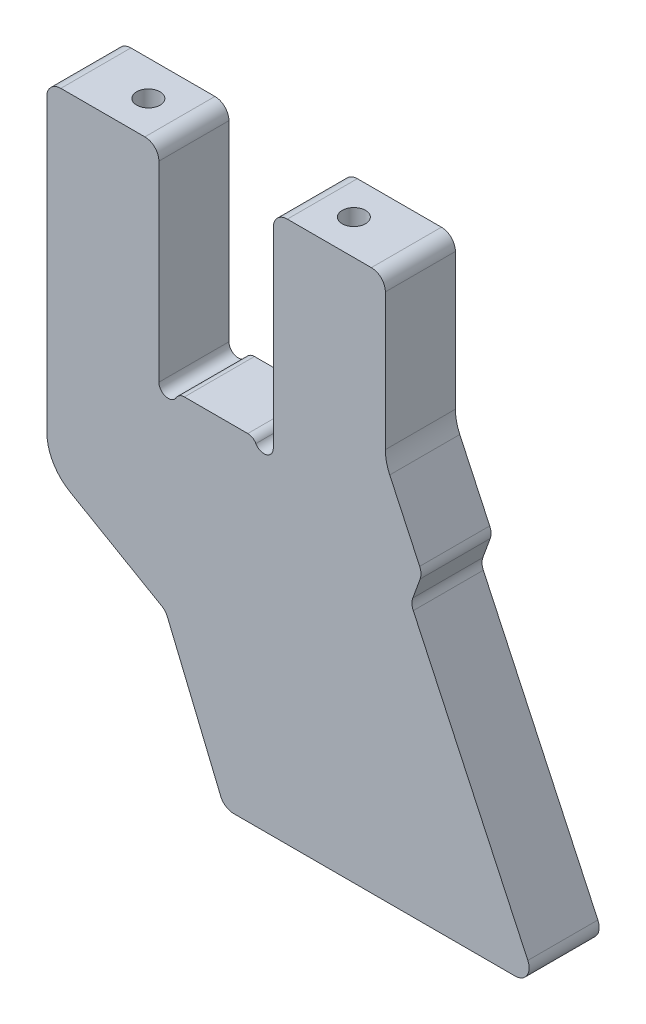
SolidWorks part; units mm, degrees
ref_plane "Plane1" through (0, 0, 0) normal (0, 0, 1) x (1, 0, 0)
ref_plane "Plane2" through (0, 0, 0) normal (0, 1, 0) x (1, 0, 0)
ref_plane "Plane3" through (0, 0, 0) normal (1, 0, 0) x (0, 0, -1)
sketch "Sketch1" plane through (0, 0, 0) normal (0, 0, 1) x (1, 0, 0)
  line L0 (0, 0) -> (0, 44) construction
  line L1 (33.25, 44) -> (15.25, 44)
  line L2 (-33.25, 44) -> (-15.25, 44)
  line L3 (6.7859, 0) -> (-6.7859, 0)
  line L4 (-11.6863, -41.1819) -> (-31.25, -29.8868)
  line L5 (3.7545, -72) -> (64.0409, -72)
  line L6 (-36.25, 41) -> (-36.25, -21.2265)
  line L7 (-10.4147, -42.6319) -> (0.9829, -70.1481)
  line L8 (42.1292, -12.8323) -> (43.6976, -8.5231)
  line L9 (12.25, 41) -> (12.25, 0)
  line L10 (-12.25, 41) -> (-12.25, 0)
  line L11 (36.25, 11.7444) -> (36.25, 41)
  line L12 (43.5974, -6.2292) -> (37.1869, 7.5182)
  line L15 (42.2293, -15.1262) -> (66.7599, -67.7321)
  arc A0 (-12.25, 41) -> (-15.25, 44) centre (-15.25, 41) ccw
  arc A1 (12.25, 0) -> (8.5179, -1) centre (10.25, 0) cw
  arc A2 (8.5179, -1) -> (6.7859, 0) centre (6.7859, -2) ccw
  arc A3 (12.25, 41) -> (15.25, 44) centre (15.25, 41) cw
  arc A4 (-8.5179, -1) -> (-6.7859, 0) centre (-6.7859, -2) cw
  arc A5 (-12.25, 0) -> (-8.5179, -1) centre (-10.25, 0) ccw
  arc A6 (-36.25, 41) -> (-33.25, 44) centre (-33.25, 41) cw
  arc A7 (36.25, 41) -> (33.25, 44) centre (33.25, 41) ccw
  arc A8 (-11.6863, -41.1819) -> (-10.4147, -42.6319) centre (-13.1863, -43.7799) cw
  arc A9 (64.0409, -72) -> (66.7599, -67.7321) centre (64.0409, -69) ccw
  arc A10 (-31.25, -29.8868) -> (-36.25, -21.2265) centre (-26.25, -21.2265) cw
  arc A11 (0.9829, -70.1481) -> (3.7545, -72) centre (3.7545, -69) ccw
  arc A12 (37.1869, 7.5182) -> (36.25, 11.7444) centre (46.25, 11.7444) cw
  arc A13 (43.6976, -8.5231) -> (43.5974, -6.2292) centre (40.8785, -7.497) ccw
  arc A14 (42.1292, -12.8323) -> (42.2293, -15.1262) centre (44.9482, -13.8584) ccw
  point P7 (-12.25, 44)
  point P22 (68.75, -72)
  point P23 (12.25, 44)
  point P28 (0, 0)
  point P31 (-36.25, -27)
  point P37 (1.75, -72)
  point P45 (36.25, -2.3035)
  point P53 (41.7042, -14)
  dimension "D2" = 22.5
  dimension "D9" = 116
  dimension "D10" = 105
  dimension "D7" = 60
  dimension "D12" = 71
  dimension "D13" = 3
  dimension "D14" = 10
  dimension "D15" = 58
  dimension "D16" = 3
  dimension "D17" = 24
  dimension "D19" = 3
  dimension "D11" = 2
  dimension "D22" = 10
  dimension "D23" = 3
  dimension "D3" = 25
  dimension "D4" = 24.5
  dimension "D5" = 67
  dimension "D6" = 72.5
  dimension "D8" = 44
  dimension "D18" = 24
  dimension "D20" = 5
  dimension "D21" = 45
extrude "Base-Extrude" add sketch "Sketch1" against normal blind 15
hole_wizard "Hole1" positions "Sketch3" profile "Sketch2" legacy
sketch "Sketch3" plane through (0, 44, 0) normal (0, 1, 0) x (-1, 0, 0)
  line L1 (15.25, -15) -> (33.25, -15) construction
  line L3 (0, 0) -> (0, -15) construction
  line L4 (-6.7859, -15) -> (6.7859, -15) construction
  point P0 (22, -7.5)
  point P6 (-22, -7.5)
  dimension "D1" = 7.5
  dimension "D2" = 44
sketch "Sketch2" plane through (-22, 44, -7.5) normal (1, 0, 0) x (0, 0, 1)
  line L0 (0, 0) -> (0, 15.5022)
  line L1 (0, 15.5022) -> (2.5, 14)
  line L2 (2.5, 14) -> (2.5, 0)
  line L4 (2.5, 0) -> (0, 0)
  line L6 (0, 15.5022) -> (-2.5, 14) construction
  line L7 (0, -4.2442) -> (0, 117.3081) construction
  dimension "Diameter" = 5
  dimension "Depth" = 14
  dimension "Drill Angle" = 118
cosmetic thread "Cosmetic Thread1" parameters "D1"=10, "D2"=6
cosmetic thread "Cosmetic Thread2" parameters "D1"=10, "D2"=6
